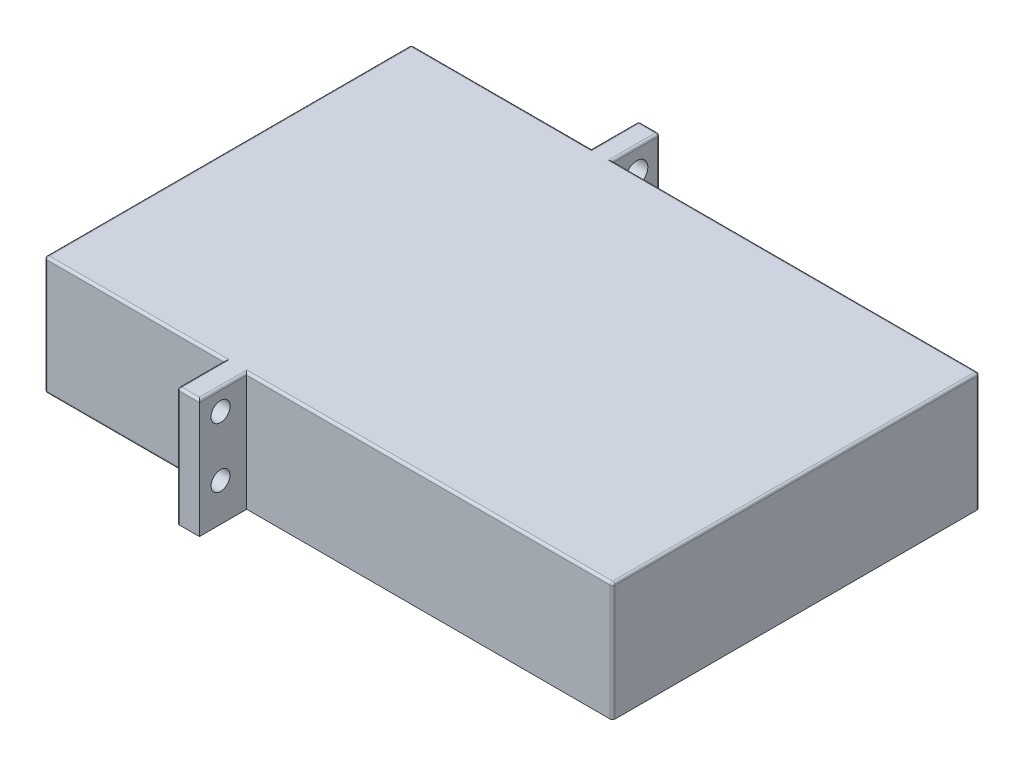
SolidWorks part; units mm, degrees
ref_plane "前视基准面" through (0, 0, 0) normal (0, 0, 1) x (1, 0, 0)
ref_plane "上视基准面" through (0, 0, 0) normal (0, 1, 0) x (1, 0, 0)
ref_plane "右视基准面" through (0, 0, 0) normal (1, 0, 0) x (0, 0, -1)
other "Configuration Table"
sketch "草图1" plane through (0, 0, 0) normal (0, 0, 1) x (1, 0, 0)
  line L1 (-12.069, 29.805) -> (35.931, 29.805)
  line L2 (-12.069, 29.805) -> (-12.069, 19.805)
  line L3 (-12.069, 19.805) -> (35.931, 19.805)
  line L4 (35.931, 29.805) -> (35.931, 19.805)
  dimension "D1" = 10
  dimension "D2" = 48
extrude "凸台-拉伸1" add sketch "草图1" along normal blind 31
sketch "草图4" plane through (0, 0, 0) normal (0, 0, -1) x (-1, 0, 0)
  line L0 (-35.931, 29.805) -> (12.069, 29.805) construction
  line L1 (-4.931, 29.805) -> (-3.142, 29.805)
  line L2 (-4.931, 29.805) -> (-4.931, 19.805)
  line L3 (-4.931, 19.805) -> (-3.142, 19.805)
  line L4 (-3.142, 29.805) -> (-3.142, 19.805)
  line L5 (12.069, 19.805) -> (-35.931, 19.805) construction
  line L6 (-35.931, 19.805) -> (-35.931, 29.805) construction
  dimension "D1" = 31
extrude "凸台-拉伸2" add sketch "草图4" along normal blind 4
sketch "草图6" plane through (3.142, 0, 0) normal (-1, 0, 0) x (0, 0, 1)
  circle A0 centre (-2.0419, 27.8174) radius 0.9369
  circle A1 centre (-2.0419, 23.0205) radius 0.8835
  dimension "D1" = 4.7969
sketch "草图13" plane through (0, 29.805, 0) normal (0, 1, 0) x (1, 0, 0)
  line L0 (3.142, 0) -> (3.142, -31) construction
  line L1 (35.931, -31) -> (-12.069, -31) construction
  line L2 (4.931, 0) -> (4.931, -31)
sketch "草图14" plane through (0, 0, 31) normal (0, 0, 1) x (1, 0, 0)
  line L0 (-12.069, 19.805) -> (35.931, 19.805) construction
  line L1 (3.142, 29.805) -> (5.014, 29.805)
  line L2 (3.142, 29.805) -> (3.142, 19.805)
  line L3 (3.142, 19.805) -> (5.014, 19.805)
  line L4 (5.014, 29.805) -> (5.014, 19.805)
extrude "凸台-拉伸4" add sketch "草图14" along normal blind 4
sketch "草图15" plane through (-12.069, 0, 0) normal (-1, 0, 0) x (0, 0, 1)
  line L0 (-2.0419, 27.8174) -> (35, 27.8174) construction
  line L1 (35, 29.805) -> (35, 19.805) construction
  line L2 (-2.0419, 23.0205) -> (35, 23.0205) construction
  line L3 (-2.0419, 27.8174) -> (-2.0419, 23.0205)
  line L4 (11.9581, 29.805) -> (11.9581, 19.805) construction
  line L5 (0, 29.805) -> (31, 29.805) construction
  line L6 (31, 19.805) -> (0, 19.805) construction
  circle A0 centre (33.0967, 27.8174) radius 0.93
  circle A1 centre (33.0967, 23.0205) radius 0.9467
  circle A2 centre (11.9581, 25.419) radius 3.6658
  point P20 (-2.0419, 25.419)
  dimension "D1" = 14
extrude "凸台-拉伸5" add sketch "草图15" along normal blind 0.5 contours A2
sketch "草图16" plane through (-12.569, 0, 0) normal (-1, 0, 0) x (0, 0, 1)
  circle A0 centre (11.9581, 25.419) radius 3.013
extrude "凸台-拉伸6" add sketch "草图16" along normal blind 0.3
sketch "草图17" plane through (-12.869, 0, 0) normal (-1, 0, 0) x (0, 0, 1)
  circle A0 centre (11.8954, 25.6383) radius 1.2361
sketch "草图19" plane through (-12.869, 0, 0) normal (-1, 0, 0) x (0, 0, 1)
extrude "凸台-拉伸8" add sketch "草图17" along normal blind 2
sketch "草图22" plane through (3.142, 0, 0) normal (-1, 0, 0) x (0, 0, 1)
  line L0 (-2.0419, 27.8174) -> (35, 27.8174) construction
  line L1 (35, 29.805) -> (35, 19.805) construction
  line L2 (-2.0419, 23.0205) -> (35, 23.0205) construction
  circle A0 centre (-2.0419, 23.0205) radius 0.8835 construction
  circle A1 centre (-2.0419, 27.8174) radius 0.9369 construction
  circle A2 centre (-2.0419, 23.0205) radius 0.8835
  circle A3 centre (-2.0419, 27.8174) radius 0.9369
extrude "切除-拉伸1" cut sketch "草图22" against normal blind 5
sketch "草图23" plane through (3.142, 0, 0) normal (-1, 0, 0) x (0, 0, 1)
  line L0 (-2.0419, 27.8174) -> (35, 28.0801) construction
  line L1 (35, 29.805) -> (35, 19.805) construction
  line L2 (-2.0419, 23.0205) -> (35, 23.0205) construction
  circle A0 centre (33.2136, 28.0675) radius 0.805
  circle A1 centre (33.2136, 23.0205) radius 0.7961
extrude "切除-拉伸2" cut sketch "草图23" against normal blind 5
fillet "圆角3" radius 0.2 1 edges at (35.931, 29.805, 15.5)
fillet "圆角4" radius 0.2 4 edges at (35.931, 24.705, 0) (35.8725, 29.7464, 0) (-4.4635, 29.805, 0) (20.331, 29.805, 0)
fillet "圆角5" radius 0.2 2 edges at (4.931, 29.805, -1.9) (3.142, 29.805, -1.9)
fillet "圆角6" radius 0.2 8 edges at (35.931, 24.705, 31) (35.8725, 29.7464, 31) (3.142, 24.705, -4) (3.2006, 29.7464, -4) (4.931, 24.705, -4) (4.8725, 29.7464, -4) (20.3725, 29.805, 31) (4.0365, 29.805, -4)
fillet "圆角7" radius 0.2 2 edges at (4.078, 29.805, 35) (5.014, 29.805, 32.9)
fillet "圆角8" radius 0.2 4 edges at (3.142, 24.705, 35) (3.142, 29.7464, 34.9414) (-4.4635, 29.805, 31) (3.142, 29.805, 32.9)
fillet "圆角9" radius 0.2 5 edges at (-12.069, 29.7464, 30.9414) (-12.069, 24.705, 0) (-12.069, 29.7464, 0.0586) (-12.069, 24.705, 31) (-12.069, 29.805, 15.5)
fillet "圆角10" radius 0.2 5 edges at (-4.3635, 19.805, 0) (-12.0104, 19.805, 0.0586) (-12.0104, 19.805, 30.9414) (-12.069, 19.805, 15.5) (-4.3635, 19.805, 31)
